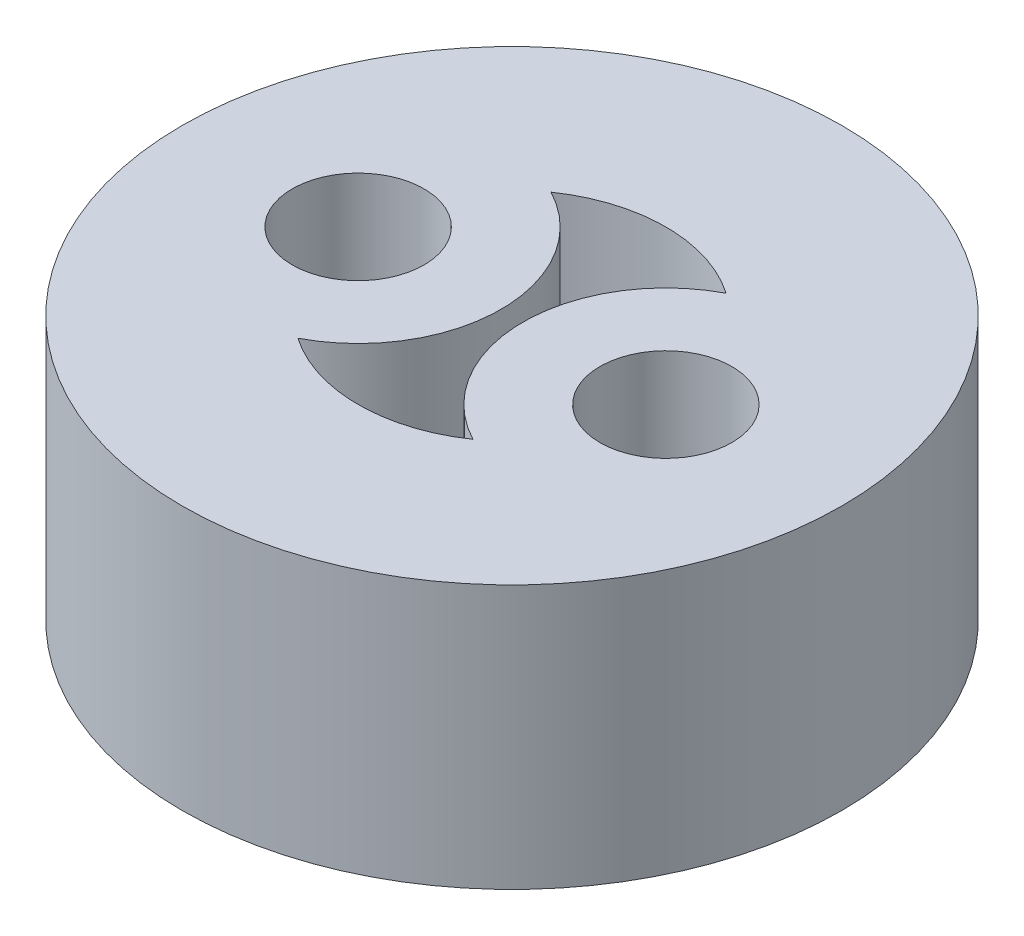
SolidWorks part; units mm, degrees
ref_plane "Plan de face" through (0, 0, 0) normal (0, 0, 1) x (1, 0, 0)
ref_plane "Plan de dessus" through (0, 0, 0) normal (0, 1, 0) x (1, 0, 0)
ref_plane "Plan de droite" through (0, 0, 0) normal (1, 0, 0) x (0, 0, -1)
sketch "Esquisse1" plane through (0, 0, 0) normal (0, 1, 0) x (1, 0, 0)
  line L0 (-3.5, 0) -> (3.5, 0) construction
  circle A0 centre (0, 0) radius 7.5
  circle A2 centre (-3.5, 0) radius 1.5
  circle A3 centre (3.5, 0) radius 1.5
  arc A4 (1.9911, 2.8785) -> (1.9911, -2.8785) centre (3.5, 0) ccw
  arc A5 (-1.9911, -2.8785) -> (-1.9911, 2.8785) centre (-3.5, 0) ccw
  arc A6 (-1.9911, -2.8785) -> (1.9911, -2.8785) centre (0, 0) ccw
  arc A9 (1.9911, 2.8785) -> (-1.9911, 2.8785) centre (0, 0) ccw
  circle A10 centre (-3.5, 0) radius 3.25 construction
  circle A11 centre (3.5, 0) radius 3.25 construction
  dimension "D1" = 15
  dimension "D2" = 6.5
  dimension "D3" = 6.5
  dimension "D4" = 7
  dimension "D5" = 3
  dimension "D6" = 3
  dimension "D7" = 3.5
  dimension "D8" = 3.5
  dimension "D9" = 3.25
  dimension "D10" = 3.25
  dimension "D11" = 3.5
extrude "Boss.-Extru.1" add sketch "Esquisse1" along normal blind 6
